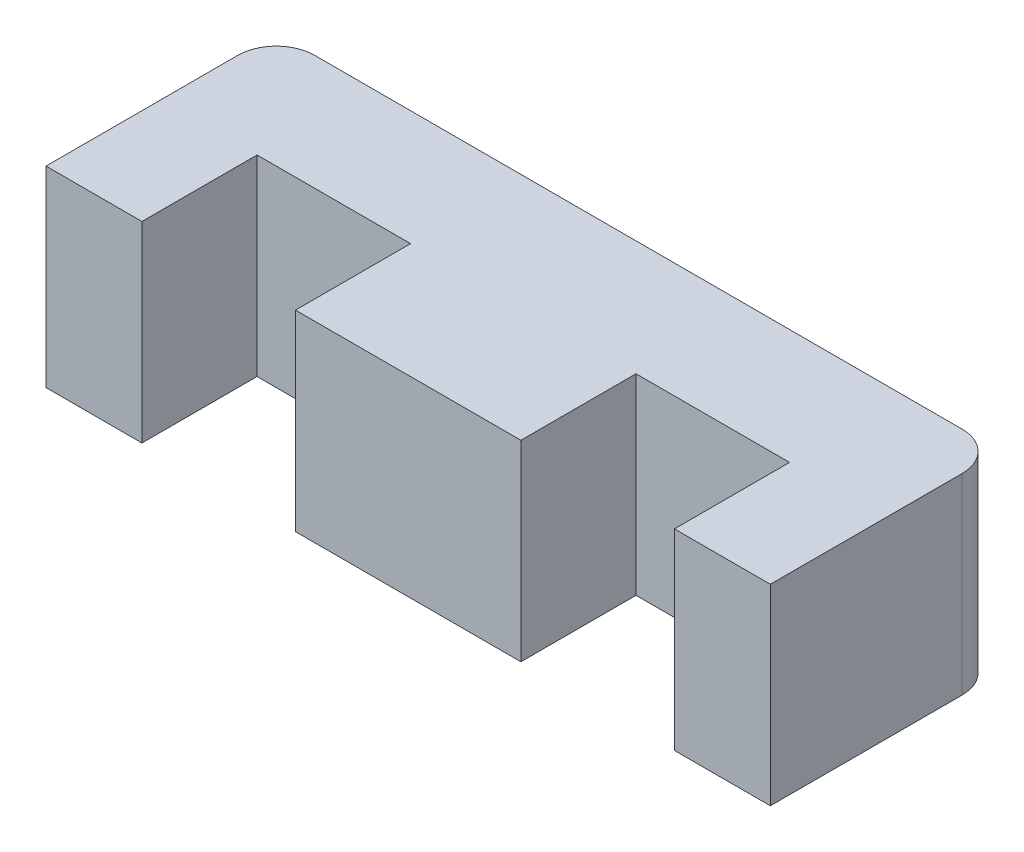
SolidWorks part; units mm, degrees
ref_plane "Front" through (0, 0, 0) normal (0, 0, 1) x (1, 0, 0)
ref_plane "Top" through (0, 0, 0) normal (0, 1, 0) x (1, 0, 0)
ref_plane "Right" through (0, 0, 0) normal (1, 0, 0) x (0, 0, -1)
sketch "Sketch1" plane through (0, 0, 0) normal (0, 1, 0) x (1, 0, 0)
  line L0 (0, 0) -> (8, 0)
  line L1 (8, 0) -> (8, -6)
  line L2 (8, -6) -> (19.75, -6)
  line L3 (19.75, -6) -> (19.75, 0)
  line L4 (19.75, 0) -> (27.75, 0)
  line L5 (27.75, 0) -> (27.75, -6)
  line L6 (27.75, -6) -> (32.75, -6)
  line L7 (32.75, -6) -> (32.75, 6)
  line L8 (32.75, 6) -> (-5, 6)
  line L9 (-5, 6) -> (-5, -6)
  line L10 (-5, -6) -> (0, -6)
  line L11 (0, -6) -> (0, 0)
  point P11 (4, 0)
  point P14 (23.75, 0)
  dimension "D1" = 19.75
  dimension "D2" = 6
  dimension "D3" = 8
  dimension "D4" = 5
  dimension "D5" = 12
extrude "Boss-Extrude1" add sketch "Sketch1" along normal blind 10
fillet "Fillet1" radius 2 2 edges at (32.75, 5, -6) (-5, 5, -6)
